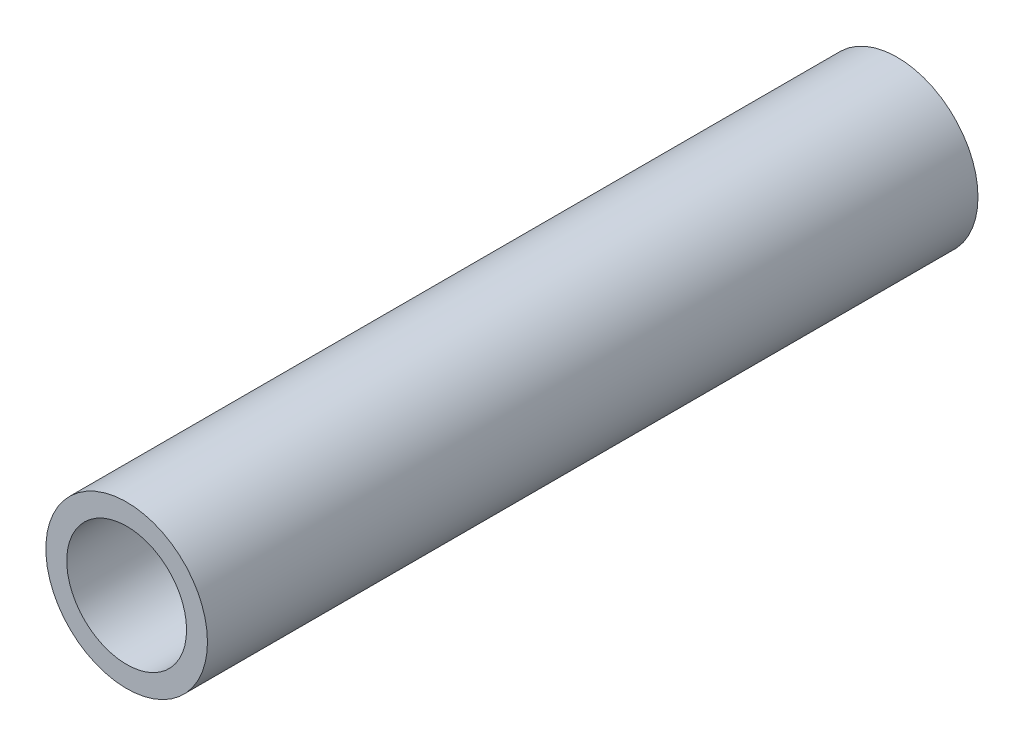
SolidWorks part; units mm, degrees
material "PVC Rigid"
ref_plane "Front Plane" through (0, 0, 0) normal (0, 0, 1) x (1, 0, 0)
ref_plane "Top Plane" through (0, 0, 0) normal (0, 1, 0) x (1, 0, 0)
ref_plane "Right Plane" through (0, 0, 0) normal (1, 0, 0) x (0, 0, -1)
sketch "Sketch1" plane through (0, 0, 0) normal (0, 0, 1) x (1, 0, 0)
  circle A0 centre (0, 0) radius 10.6553
  circle A2 centre (0, 0) radius 7.8994
  dimension "D1" = 21.3106
  dimension "D2" = 15.7988
extrude "Boss-Extrude1" add sketch "Sketch1" along normal blind 101.6
